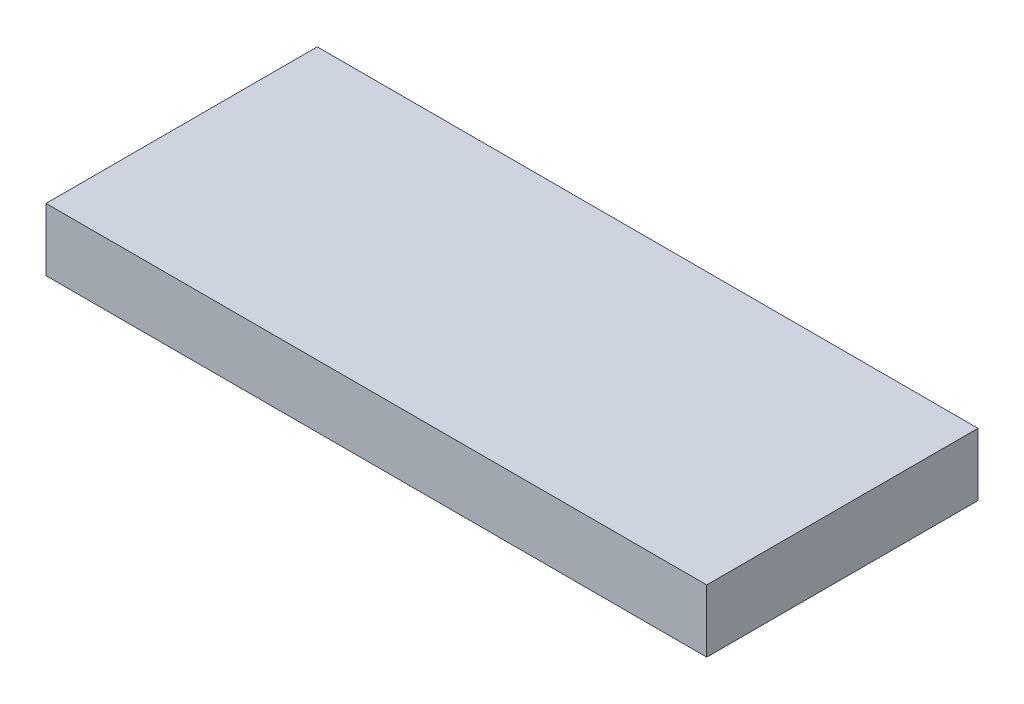
SolidWorks part; units mm, degrees
ref_plane "Front Plane" through (0, 0, 0) normal (0, 0, 1) x (1, 0, 0)
ref_plane "Top Plane" through (0, 0, 0) normal (0, 1, 0) x (1, 0, 0)
ref_plane "Right Plane" through (0, 0, 0) normal (1, 0, 0) x (0, 0, -1)
sketch "Sketch1" plane through (0, 0, 0) normal (0, 1, 0) x (1, 0, 0)
  line L1 (-23.75, 9.75) -> (23.75, 9.75)
  line L2 (-23.75, 9.75) -> (-23.75, -9.75)
  line L3 (-23.75, -9.75) -> (23.75, -9.75)
  line L4 (23.75, 9.75) -> (23.75, -9.75)
  line L5 (-23.75, 9.75) -> (23.75, -9.75) construction
  line L6 (-23.75, -9.75) -> (23.75, 9.75) construction
  point P0 (0, 0)
  dimension "D1" = 47.5
  dimension "D2" = 19.5
extrude "Boss-Extrude1" add sketch "Sketch1" along normal blind 4.5
